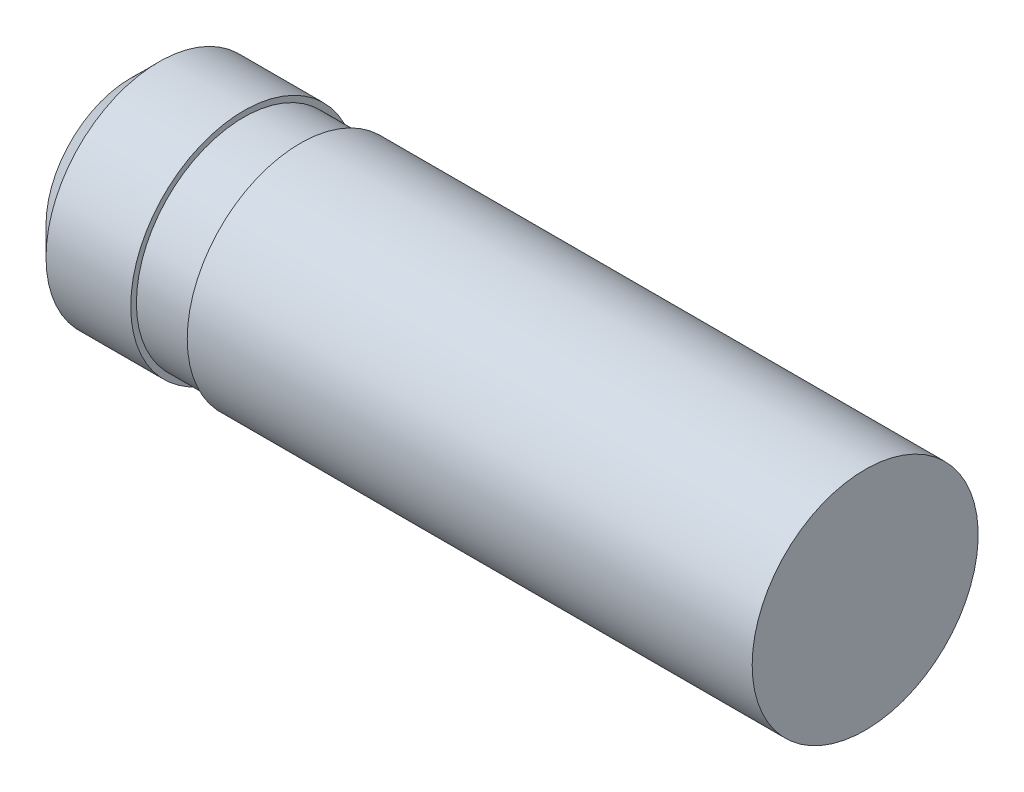
SolidWorks part; units mm, degrees
ref_plane "Front Plane" through (0, 0, 0) normal (0, 0, 1) x (1, 0, 0)
ref_plane "Top Plane" through (0, 0, 0) normal (0, 1, 0) x (1, 0, 0)
ref_plane "Right Plane" through (0, 0, 0) normal (1, 0, 0) x (0, 0, -1)
sketch "Эскиз1" plane through (0, 0, 0) normal (0, 0, 1) x (1, 0, 0)
  line L0 (0, 0) -> (16.2693, 0) construction
  line L1 (0, 0) -> (0, 1.5)
  line L2 (0.5, 2) -> (2, 2)
  line L3 (13, 2) -> (13, 0)
  line L4 (0, 1.5) -> (0.5, 2)
  line L5 (0, 0) -> (13, 0)
  line L6 (2, 2) -> (2, 1.9)
  line L7 (3, 2) -> (3, 1.9)
  line L8 (2, 1.9) -> (3, 1.9)
  line L9 (3, 2) -> (13, 2)
  point P3 (0, 2)
  point P10 (0, 0.75)
  dimension "D1" = 13
  dimension "D2" = 2
  dimension "D3" = 0.5
  dimension "D4" = 45
  dimension "D5" = 2
  dimension "D6" = 1
  dimension "D7" = 3.8
revolve "Повернуть1" add sketch "Эскиз1" angle 360 about L0
